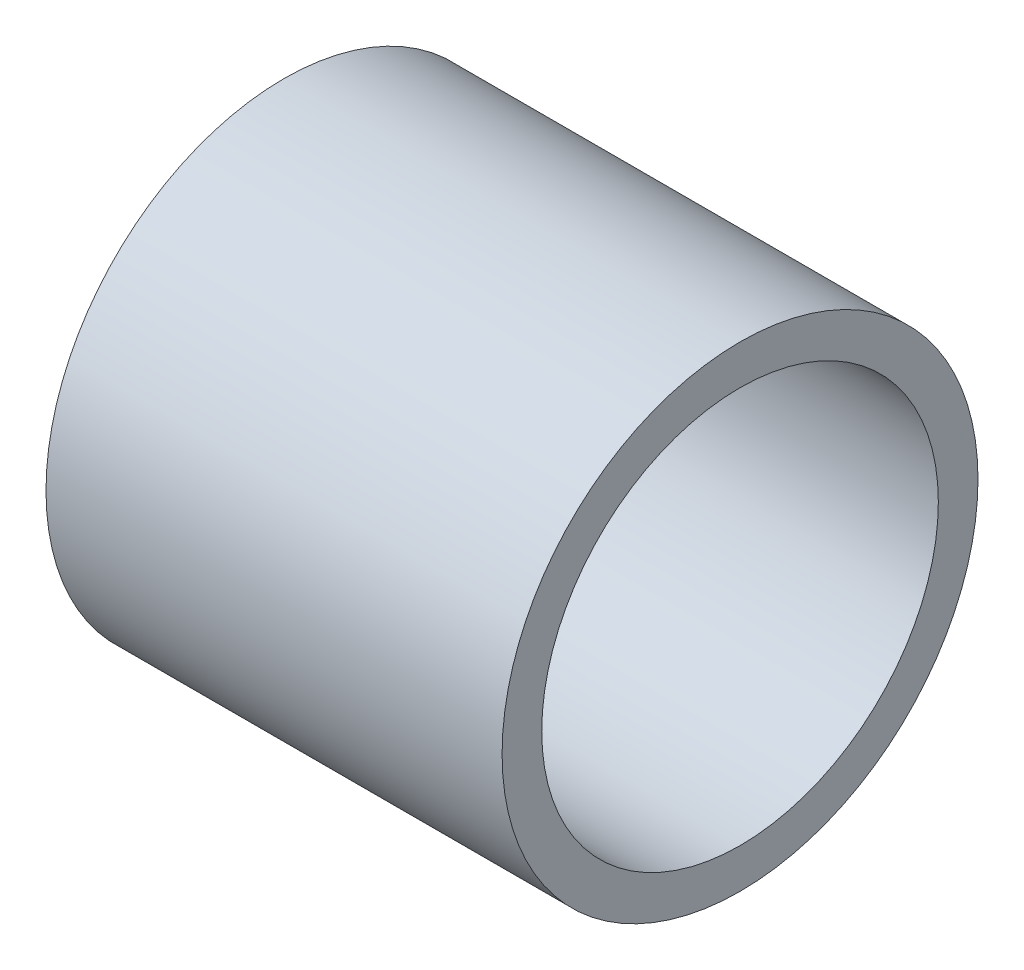
SolidWorks part; units mm, degrees
ref_plane "前基準面" through (0, 0, 0) normal (0, 0, 1) x (1, 0, 0)
ref_plane "上基準面" through (0, 0, 0) normal (0, 1, 0) x (1, 0, 0)
ref_plane "右基準面" through (0, 0, 0) normal (1, 0, 0) x (0, 0, -1)
sketch "草圖1" plane through (0, 0, 0) normal (1, 0, 0) x (0, 0, -1)
  circle A0 centre (0, 0) radius 6
extrude "填料-伸長1" add sketch "草圖1" along normal blind 13
sketch "草圖2" plane through (0, 0, 0) normal (0, 1, 0) x (1, 0, 0)
  line L0 (0, 0) -> (1.5, 6)
  line L1 (13, 6) -> (0, 6) construction
  line L2 (1.5, 6) -> (0, 6) construction
  line L3 (0, 6) -> (0, 0) construction
  line L4 (1.0029, 0) -> (-1.0029, 0) construction
  line L5 (0, 0) -> (-0.4626, 0)
  line L6 (-0.4626, 0) -> (-0.4626, 6.4964)
  line L7 (-0.4626, 6.4964) -> (1.5, 6.4964)
  line L8 (1.5, 6.4964) -> (1.5, 6)
  point P9 (0, 0)
  dimension "D1" = 1.5
revolve "除料-旋轉2" cut sketch "草圖2" angle 360 about L4
shell "薄殼1" thickness 1
